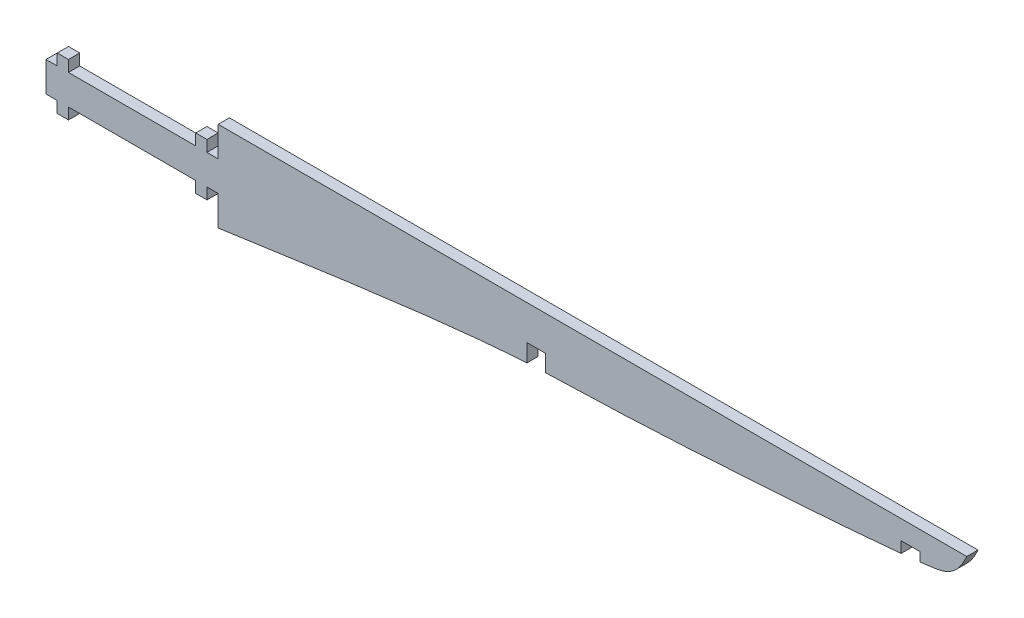
SolidWorks part; units mm, degrees
material "PC High Viscosity"
ref_plane "Front Plane" through (0, 0, 0) normal (0, 0, 1) x (1, 0, 0)
ref_plane "Top Plane" through (0, 0, 0) normal (0, 1, 0) x (1, 0, 0)
ref_plane "Right Plane" through (0, 0, 0) normal (1, 0, 0) x (0, 0, -1)
sketch "Sketch1" plane through (0, 0, 0) normal (0, 0, 1) x (1, 0, 0)
  line L0 (23, 0) -> (-23, 0) construction
  line L1 (-23, -4) -> (23, -4)
  line L2 (-23, -4) -> (-23, 4)
  line L3 (-23, 4) -> (23, 4)
  line L4 (23, -4) -> (23, 4)
  line L5 (-23, -4) -> (23, 4) construction
  line L6 (-23, 4) -> (23, -4) construction
  line L7 (17, 7) -> (20, 7)
  line L8 (17, 7) -> (17, -7)
  line L9 (17, -7) -> (20, -7)
  line L10 (20, 7) -> (20, -7)
  line L11 (0, 4) -> (0, -4) construction
  line L12 (-20, 7) -> (-20, -7)
  line L13 (-17, -7) -> (-20, -7)
  line L14 (-17, 7) -> (-17, -7)
  line L15 (-17, 7) -> (-20, 7)
  point P0 (0, 0)
  dimension "D1" = 8
  dimension "D2" = 46
  dimension "D3" = 3
  dimension "D4" = 3
  dimension "D5" = 3
extrude "Boss-Extrude1" add sketch "Sketch1" along normal blind 3 contours L14 L15 L12 L3 | L12 L3 L2 L1 | L14 L3 L12 L1 | L14 L1 L12 L13 | L3 L14 L1 L8 | L3 L10 L1 L4 | L10 L3 L8 L1 | L10 L7 L8 L3 | L10 L1 L8 L9
sketch "Sketch2" plane through (0, 0, 3) normal (0, 0, 1) x (1, 0, 0)
  line L0 (23, -12) -> (23, 12)
  line L1 (23, 12) -> (223, 12)
  line L2 (23, -4) -> (23, 4) construction
  line L3 (-23, 0) -> (23, 0) construction
  line L4 (-23, -4) -> (-23, 4) construction
  spline S0 degree 3 poles (223, 12) (221.1406, 7.8923) (218.7021, 6.1959) (212.7902, 3.9314) (103.0667, -3.7389) (102.0093, -0.4994) (23, -12) knots 0 0 0 0 0.169853 0.232552 0.58317 1 1 1 1
  dimension "D1" = 200
  dimension "D2" = 24
extrude "Boss-Extrude2" add sketch "Sketch2" against normal up to surface (3 mm away) up to face at (0, 0, 0)
sketch "Sketch4" plane through (0, 0, 3) normal (0, 0, 1) x (1, 0, 0)
  line L1 (105.4565, -8.7611) -> (110.4565, -8.7611)
  line L2 (105.4565, -8.7611) -> (105.4565, 2.7439)
  line L3 (105.4565, 2.7439) -> (110.4565, 2.7439)
  line L4 (110.4565, -8.7611) -> (110.4565, 2.7439)
  line L5 (205.4565, -8.7611) -> (210.4565, -8.7611)
  line L6 (205.4565, -8.7611) -> (205.4565, 6.8775)
  line L7 (205.4565, 6.8775) -> (210.4565, 6.8775)
  line L8 (210.4565, -8.7611) -> (210.4565, 6.8775)
  dimension "D1" = 5
  dimension "D2" = 100
extrude "Cut-Extrude1" cut sketch "Sketch4" against normal through all
equation "\"pulley_pitch_diam\"= 12.73mm"
equation "\"pulley_total_width\"= 16mm"
equation "\"pulley_total_diam\"= 16mm"
equation "\"belt_width\"= 6mm"
equation "\"material_thickness\"= 3mm"
equation "\"shaft_diam\"= 8mm"
equation "\"bearing_od\"= 22mm"
equation "\"bearing_thickness\"= 7mm"
equation "\"D1@Boss-Extrude1\"=\"material_thickness\""
equation "\"D5@Sketch1\"=\"material_thickness\""
